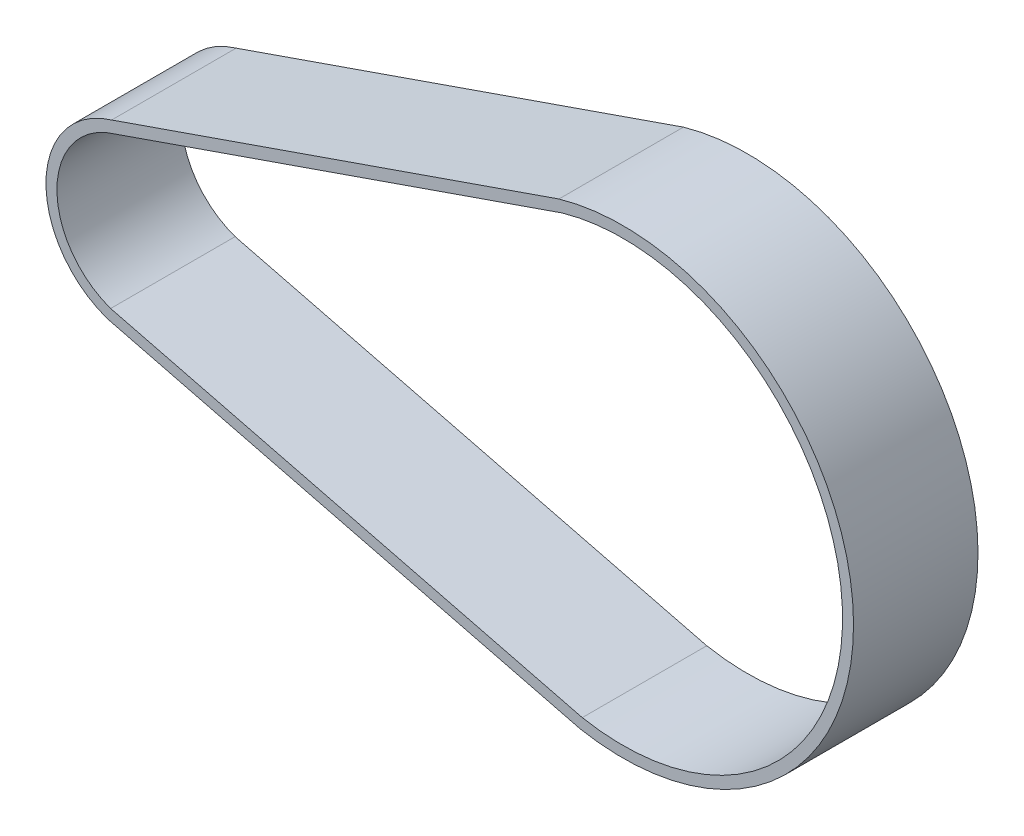
SolidWorks part; units mm, degrees
material "Rubber"
ref_plane "Front Plane" through (0, 0, 0) normal (0, 0, 1) x (1, 0, 0)
ref_plane "Top Plane" through (0, 0, 0) normal (0, 1, 0) x (1, 0, 0)
ref_plane "Right Plane" through (0, 0, 0) normal (1, 0, 0) x (0, 0, -1)
sketch "Sketch1" plane through (0, 0, 0) normal (0, 0, 1) x (1, 0, 0)
  line L0 (-3.0704, 10.5628) -> (58.0168, 31.7631)
  line L5 (60.7498, -26.5551) -> (-3.6624, -10.3724)
  line L6 (-3.5272, 11.992) -> (57.5632, 33.1934)
  line L7 (60.4275, -28.0207) -> (-4.0937, -11.8107)
  arc A4 (-3.0704, 10.5628) -> (-3.6624, -10.3724) centre (0, 0) ccw
  arc A5 (60.7498, -26.5551) -> (58.0168, 31.7631) centre (66.2952, 2.9279) ccw
  arc A6 (60.4275, -28.0207) -> (57.5632, 33.1934) centre (66.2952, 2.9279) ccw
  arc A7 (-3.5272, 11.992) -> (-4.0937, -11.8107) centre (0, 0) ccw
  arc A8 (60.7498, -26.5551) -> (58.0168, 31.7631) centre (66.2952, 2.9279) ccw construction
  point P3 (92.7974, -2.774)
  point P6 (-2.1076, 10.846)
  point P14 (-2.2351, -10.826)
  point P15 (92.9479, -3.1136)
  point P17 (59.055, 26.1846)
  point P18 (60.3709, -26.837)
  point P19 (-3.0705, 11.992)
  point P20 (-4.0937, -10.3724)
  dimension "D2" = 30
  dimension "D3" = 11
  dimension "D5" = 267
  dimension "D4" = 1.5
extrude "Boss-Extrude1" add sketch "Sketch1" along normal blind 17
